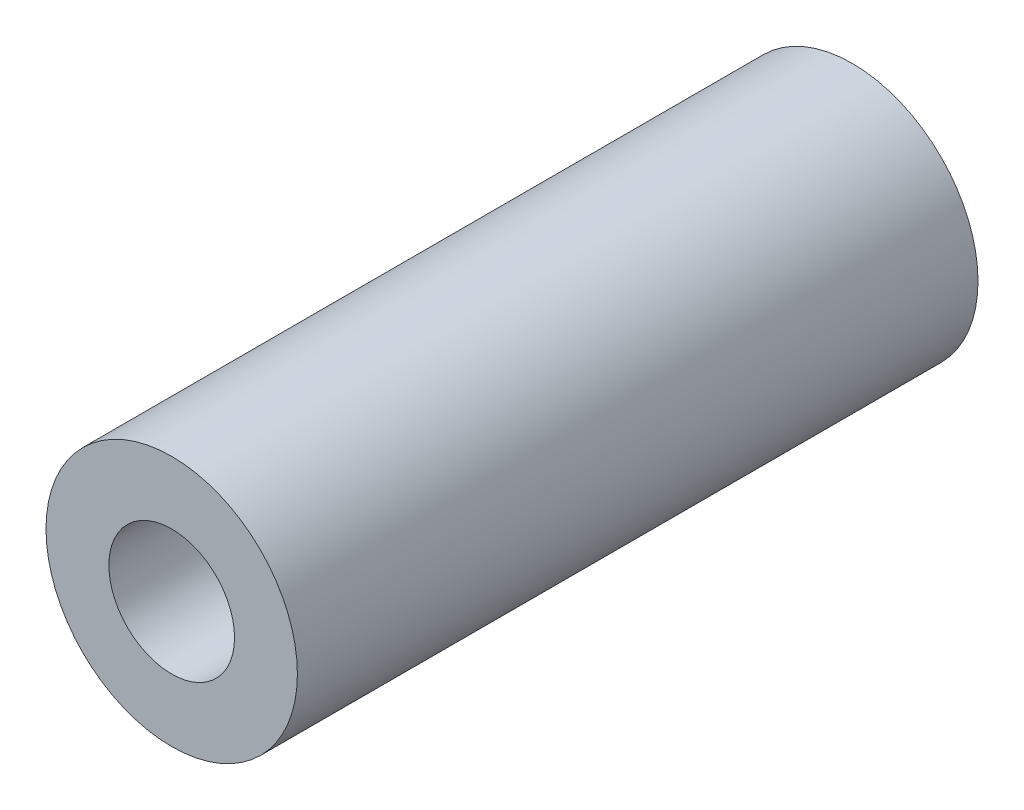
SolidWorks part; units mm, degrees
material "6061-T6 (SS)"
ref_plane "Front Plane" through (0, 0, 0) normal (0, 0, 1) x (1, 0, 0)
ref_plane "Top Plane" through (0, 0, 0) normal (0, 1, 0) x (1, 0, 0)
ref_plane "Right Plane" through (0, 0, 0) normal (1, 0, 0) x (0, 0, -1)
sketch "Sketch2" plane through (0, 0, 0) normal (0, 0, 1) x (1, 0, 0)
  circle A0 centre (0, 0) radius 3.175
  circle A1 centre (0, 0) radius 6.35
  dimension "D2" = 6.35
  dimension "D1" = 12.7
extrude "Boss-Extrude1" add sketch "Sketch2" along normal blind 34.3834
equation "\"Thick\"= .1"
equation "\"ID\"= .26"
equation "\"Length\"= 1.90367813in"
equation "\"D1@Boss-Extrude1\"  = 1.35367813in"
equation "\"D2@Sketch2\"= .25"
